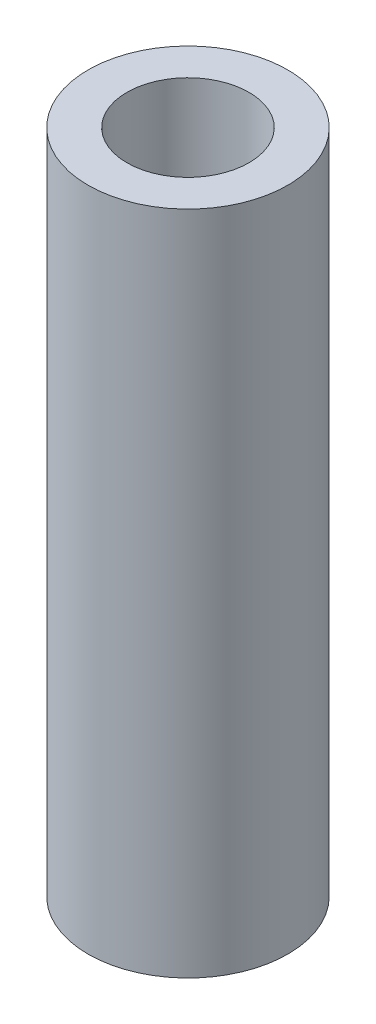
SolidWorks part; units mm, degrees
ref_plane "Front Plane" through (0, 0, 0) normal (0, 0, 1) x (1, 0, 0)
ref_plane "Top Plane" through (0, 0, 0) normal (0, 1, 0) x (1, 0, 0)
ref_plane "Right Plane" through (0, 0, 0) normal (1, 0, 0) x (0, 0, -1)
sketch "Sketch2" plane through (0, 0, 0) normal (0, 1, 0) x (1, 0, 0)
  circle A0 centre (0, 0) radius 2.75
  circle A1 centre (0, 0) radius 4.5
extrude "Boss-Extrude1" add sketch "Sketch2" along normal blind 30
